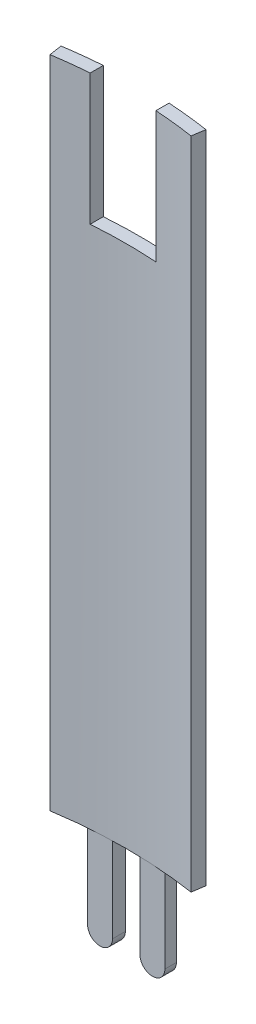
SolidWorks part; units mm, degrees
ref_plane "Front Plane" through (0, 0, 0) normal (0, 0, 1) x (1, 0, 0)
ref_plane "Top Plane" through (0, 0, 0) normal (0, 1, 0) x (1, 0, 0)
ref_plane "Right Plane" through (0, 0, 0) normal (1, 0, 0) x (0, 0, -1)
sketch "Sketch1" plane through (0, 0, 0) normal (0, 1, 0) x (1, 0, 0)
  line L0 (-14.1051, 90.9882) -> (-13.716, 88.4782)
  line L1 (13.6088, 88.4947) -> (13.9949, 91.0052)
  line L2 (0, 0) -> (-13.716, 88.4782) construction
  line L3 (0, 0) -> (0, 89.535) construction
  arc A2 (-13.716, 88.4782) -> (13.6088, 88.4947) centre (0, 0) cw
  arc A3 (-14.1051, 90.9882) -> (13.9949, 91.0052) centre (0, 0) cw
  dimension "D1" = 89.535
  dimension "D2" = 92.075
  dimension "D3" = 27.432
  dimension "D4" = 13.716
extrude "Boss-Extrude1" add sketch "Sketch1" along normal blind 127
sketch "Sketch7" plane through (0, 0, 0) normal (0, 0, 1) x (1, 0, 0)
  line L0 (5.08, -16.51) -> (5.08, 8.89) construction
  line L1 (2.667, -16.51) -> (2.667, 8.89)
  line L2 (7.493, -16.51) -> (7.493, 8.89)
  line L3 (-5.08, -16.51) -> (-5.08, 8.89) construction
  line L4 (-14.1051, 0) -> (13.9949, 0) construction
  line L5 (-7.493, -16.51) -> (-7.493, 8.89)
  line L6 (-14.1051, 0) -> (13.9949, 0)
  line L7 (-14.1051, 0) -> (13.9949, 0)
  line L8 (-13.716, 0) -> (13.6088, 0) construction
  line L9 (-13.716, 0) -> (13.6088, 0)
  line L10 (-2.667, -16.51) -> (-2.667, 8.89)
  arc A0 (2.667, -16.51) -> (7.493, -16.51) centre (5.08, -16.51) ccw
  arc A1 (7.493, 8.89) -> (2.667, 8.89) centre (5.08, 8.89) ccw
  arc A2 (-7.493, -16.51) -> (-2.667, -16.51) centre (-5.08, -16.51) ccw
  arc A3 (-2.667, 8.89) -> (-7.493, 8.89) centre (-5.08, 8.89) ccw
  point P2 (5.08, -3.81)
  point P14 (0, 0)
  point P15 (-5.08, -3.81)
  dimension "D2" = 4.826
  dimension "D1" = 25.4
  dimension "D3" = 16.51
  dimension "D4" = 5.08
  dimension "D5" = 10.16
extrude "Boss-Extrude5" add sketch "Sketch7" against normal up to surface (2.2346 mm away) from offset 89.535 offset against normal yes
sketch "Sketch9" plane through (0, 0, 0) normal (0, 0, 1) x (1, 0, 0)
  line L1 (5.9609, 127) -> (-6.7391, 127)
  line L2 (5.9609, 127) -> (5.9609, 101.6)
  line L3 (5.9609, 101.6) -> (-6.7391, 101.6)
  line L4 (-6.7391, 127) -> (-6.7391, 101.6)
  line L5 (5.9609, 127) -> (-6.7391, 101.6) construction
  line L6 (5.9609, 101.6) -> (-6.7391, 127) construction
  line L8 (-14.1051, 127) -> (-14.1051, 0) construction
  point P0 (-0.3891, 114.3)
  dimension "D1" = 25.4
  dimension "D2" = 25.4
  dimension "D3" = 12.7
  dimension "D4" = 13.716
extrude "Cut-Extrude4" cut sketch "Sketch9" against normal up to surface (91.8818 mm away)
